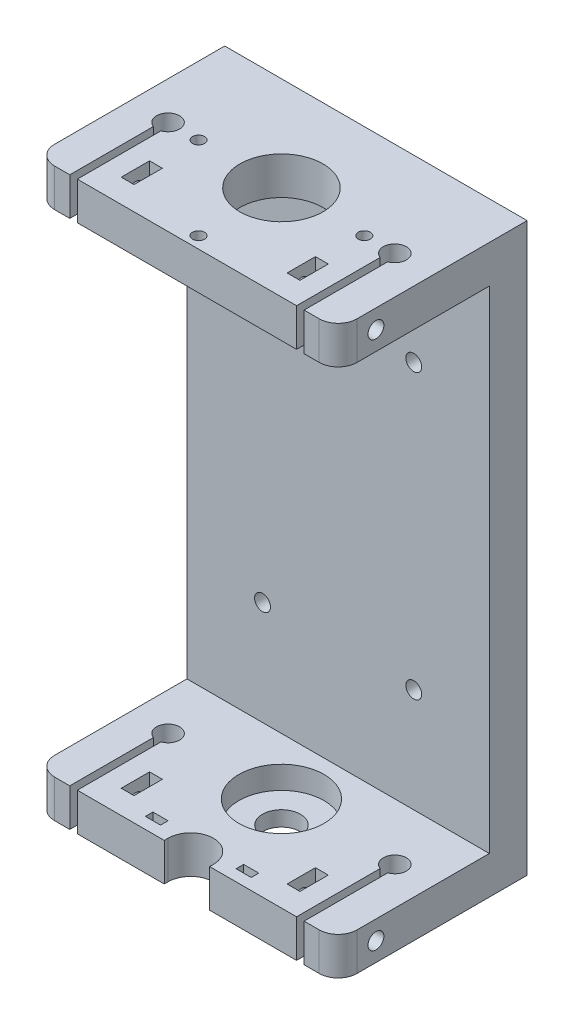
SolidWorks part; units mm, degrees
ref_plane "前基準面" through (0, 0, 0) normal (0, 0, 1) x (1, 0, 0)
ref_plane "上基準面" through (0, 0, 0) normal (0, 1, 0) x (1, 0, 0)
ref_plane "右基準面" through (0, 0, 0) normal (1, 0, 0) x (0, 0, -1)
sketch "草圖1" plane through (0, 0, 0) normal (0, 0, 1) x (1, 0, 0)
  line L1 (-40, 75) -> (40, 75)
  line L2 (-40, 75) -> (-40, -75)
  line L3 (-40, -75) -> (40, -75)
  line L4 (40, 75) -> (40, -75)
  line L5 (-40, 75) -> (40, -75) construction
  line L6 (-40, -75) -> (40, 75) construction
  point P0 (0, 0)
  dimension "D1" = 150
  dimension "D2" = 80
extrude "填料-伸長1" add sketch "草圖1" along normal blind 10
sketch "草圖4" plane through (0, -75, 0) normal (0, -1, 0) x (1, 0, 0)
  line L0 (0, 0) -> (0, 37.8464) construction
  line L1 (-40, 10) -> (40, 10)
  line L2 (-40, 10) -> (-40, 50)
  line L3 (-40, 50) -> (-31, 50)
  line L4 (40, 10) -> (40, 50)
  line L5 (-29, 50) -> (-6, 50)
  line L7 (-31, 50) -> (-31, 27.8814)
  line L9 (-29, 50) -> (-29, 27.8814)
  line L10 (29, 50) -> (29, 27.8814)
  line L11 (31, 50) -> (31, 27.8814)
  line L12 (31, 50) -> (40, 50)
  line L13 (-30, 25) -> (30, 25) construction
  line L14 (-6, 49) -> (-6, 50)
  line L16 (6, 49) -> (6, 50)
  line L17 (6, 50) -> (29, 50)
  arc A0 (-31, 27.8814) -> (-29, 27.8814) centre (-30, 25) ccw
  arc A1 (29, 27.8814) -> (31, 27.8814) centre (30, 25) ccw
  circle A2 centre (0, 25) radius 11.25
  circle A3 centre (0, 25) radius 5
  arc A4 (-6, 49) -> (6, 49) centre (0, 49) ccw
  point P13 (-30, 50)
  line M18 (40, 10) -> (-40, 10)
  dimension "D2" = 6.1
  dimension "D5" = 22.5
  dimension "D6" = 10
  dimension "D7" = 12
  dimension "D1" = 40
  dimension "D3" = 15
  dimension "D4" = 10
  dimension "D8" = 1
  dimension "D9" = 60
extrude "填料-伸長3" add sketch "草圖4" against normal blind 10 contours A4 L14 L5 L9 A0 L7 L3 L2 L4 L12 L11 A1 L10 L17 L16 A2 M18
sketch "草圖5" plane through (0, -75, 0) normal (0, -1, 0) x (1, 0, 0)
  circle A0 centre (0, 25) radius 11.25
  circle A1 centre (0, 25) radius 5
  dimension "D1" = 10
  dimension "D2" = 22.5
extrude "填料-伸長4" add sketch "草圖5" against normal blind 4
sketch "草圖6" plane through (40, 0, 0) normal (1, 0, 0) x (0, 0, -1)
  line L0 (-50, -65) -> (-50, -75) construction
  circle A0 centre (-40, -70) radius 2.1
  dimension "D2" = 4.2
  dimension "D1" = 10
extrude "除料-伸長1" cut sketch "草圖6" against normal blind 24
sketch "草圖7" plane through (0, -75, 0) normal (0, -1, 0) x (1, 0, 0)
  line L0 (16, 40) -> (21.9431, 40) construction
  line L1 (16, 37.9) -> (16, 42.1) construction
  line L2 (21.9431, 40) -> (0, 24.9665) construction
  line L3 (0, 24.9665) -> (0, 53.0789) construction
  line L4 (-20.2431, 36.25) -> (-20.2431, 43.75)
  line L5 (20.2431, 36.25) -> (23.6431, 36.25)
  line L6 (20.2431, 36.25) -> (20.2431, 43.75)
  line L7 (20.2431, 43.75) -> (23.6431, 43.75)
  line L8 (23.6431, 36.25) -> (23.6431, 43.75)
  line L9 (20.2431, 36.25) -> (23.6431, 43.75) construction
  line L10 (20.2431, 43.75) -> (23.6431, 36.25) construction
  line L11 (-20.2431, 36.25) -> (-23.6431, 36.25)
  line L12 (-23.6431, 36.25) -> (-23.6431, 43.75)
  line L13 (-20.2431, 43.75) -> (-23.6431, 43.75)
  dimension "D1" = 3.4
  dimension "D2" = 7.5
extrude "除料-伸長2" cut sketch "草圖7" against normal blind 24
sketch "草圖8" plane through (-40, 0, 0) normal (-1, 0, 0) x (0, 0, 1)
  circle A0 centre (40, -70) radius 2.1
extrude "除料-伸長3" cut sketch "草圖8" against normal blind 24
sketch "草圖9" plane through (0, 75, 0) normal (0, 1, 0) x (1, 0, 0)
  line L0 (0, 0) -> (0, -54.0504) construction
  line L1 (-40, -10) -> (40, -10)
  line L2 (-40, -10) -> (-40, -50)
  line L3 (-40, -50) -> (40, -50)
  line L4 (40, -10) -> (40, -50)
  line L6 (-21.9203, -25) -> (0, -46.9203) construction
  line L7 (-21.9203, -25) -> (0, -3.0797) construction
  line L8 (0, -3.0797) -> (21.9203, -25) construction
  line L9 (0, -46.9203) -> (21.9203, -25) construction
  line L10 (-21.9203, -25) -> (21.9203, -25) construction
  line L11 (0, -3.0797) -> (0, -46.9203) construction
  circle A0 centre (0, -25) radius 5 construction
  circle A1 centre (0, -25) radius 5 construction
  circle A2 centre (0, -25) radius 11
  circle A3 centre (-21.9203, -25) radius 1.6
  circle A4 centre (0, -46.9203) radius 1.6
  circle A5 centre (21.9203, -25) radius 1.6
  dimension "D1" = 22
  dimension "D3" = 3.2
  dimension "D2" = 31
extrude "填料-伸長5" add sketch "草圖9" against normal blind 10 contours L2 L1 L4 L3 | A2 | A3 | A5 | A4
fillet "圓角1" radius 5 4 edges at (-40, -70, 50) (-40, 70, 50) (40, -70, 50) (40, 70, 50)
sketch "草圖10" plane through (0, 75, 0) normal (0, 1, 0) x (1, 0, 0)
  line L0 (-35, -50) -> (35, -50) construction
  line L1 (-30.9921, -72.1172) -> (-29, -72.1172)
  line L2 (-30.9921, -72.1172) -> (-30.9921, -27.8841)
  line L4 (-29, -72.1172) -> (-29, -27.8814)
  line L5 (-30.9921, -72.1172) -> (-29, -27.8814) construction
  line L6 (-30.9921, -27.8841) -> (-29, -72.1172) construction
  line L8 (29.0016, -72.1183) -> (31, -72.1183)
  line L9 (29.0016, -72.1183) -> (29.0016, -27.882)
  line L11 (31, -72.1183) -> (31, -27.8814)
  line L12 (29.0016, -72.1183) -> (31, -27.8814) construction
  line L13 (29.0016, -27.882) -> (31, -72.1183) construction
  line L14 (-23.6431, -36.25) -> (-20.2431, -36.25)
  line L15 (-23.6431, -36.25) -> (-23.6431, -43.75)
  line L16 (-23.6431, -43.75) -> (-20.2431, -43.75)
  line L17 (-20.2431, -36.25) -> (-20.2431, -43.75)
  line L18 (20.2431, -36.25) -> (23.6431, -36.25)
  line L19 (20.2431, -36.25) -> (20.2431, -43.75)
  line L20 (20.2431, -43.75) -> (23.6431, -43.75)
  line L21 (23.6431, -36.25) -> (23.6431, -43.75)
  arc A0 (-29, -27.8814) -> (-30.9921, -27.8841) centre (-30, -25) ccw
  arc A1 (31, -27.8814) -> (29.0016, -27.882) centre (30, -25) ccw
  point P6 (-29.9961, -50)
  point P14 (30.0008, -50)
extrude "除料-伸長5" cut sketch "草圖10" against normal blind 10 contours L2 A0 L4 L1 | L15 L14 L17 L16 | L19 L18 L21 L20 | L9 A1 L11 L8
sketch "草圖11" plane through (40, 0, 0) normal (1, 0, 0) x (0, 0, -1)
  line L0 (-40, -70) -> (-40, 84.814) construction
  circle A0 centre (-40, 70) radius 2.1
  dimension "D1" = 4.2
extrude "除料-伸長6" cut sketch "草圖11" against normal blind 24
sketch "草圖12" plane through (-40, 0, 0) normal (-1, 0, 0) x (0, 0, 1)
  circle A0 centre (40, 70) radius 2.1
extrude "除料-伸長7" cut sketch "草圖12" against normal blind 24
sketch "草圖14" plane through (0, -75, 0) normal (0, -1, 0) x (1, 0, 0)
  line L0 (0, 49) -> (0, 57.7275) construction
  line L1 (-12, 53.5876) -> (-12, 37.2144) construction
  line L2 (-29, 50) -> (-6, 50) construction
  line L3 (-14, 45) -> (-10, 45)
  line L4 (-14, 45) -> (-14, 47)
  line L5 (-14, 47) -> (-10, 47)
  line L6 (-10, 45) -> (-10, 47)
  line L7 (-14, 45) -> (-10, 47) construction
  line L8 (-14, 47) -> (-10, 45) construction
  line L9 (14, 45) -> (10, 45)
  line L10 (10, 45) -> (10, 47)
  line L11 (14, 47) -> (10, 47)
  line L12 (14, 45) -> (14, 47)
  point P6 (-12, 46)
  dimension "D1" = 4
  dimension "D2" = 2
  dimension "D3" = 12
  dimension "D4" = 4
extrude "除料-伸長9" cut sketch "草圖14" against normal blind 10
sketch "草圖16" plane through (0, 0, 10) normal (0, 0, 1) x (1, 0, 0)
  line L1 (-20, -37.5) -> (20, -37.5) construction
  line L2 (-20, -37.5) -> (-20, 37.5) construction
  line L3 (-20, 37.5) -> (20, 37.5) construction
  line L4 (20, -37.5) -> (20, 37.5) construction
  line L5 (-20, -37.5) -> (20, 37.5) construction
  line L6 (-20, 37.5) -> (20, -37.5) construction
  circle A0 centre (-20, 37.5) radius 2.1
  circle A1 centre (20, 37.5) radius 2.1
  circle A2 centre (20, -37.5) radius 2.1
  circle A3 centre (-20, -37.5) radius 2.1
  point P0 (0, 0)
  dimension "D3" = 4.2
  dimension "D1" = 40
  dimension "D2" = 75
extrude "除料-伸長10" cut sketch "草圖16" against normal through all
